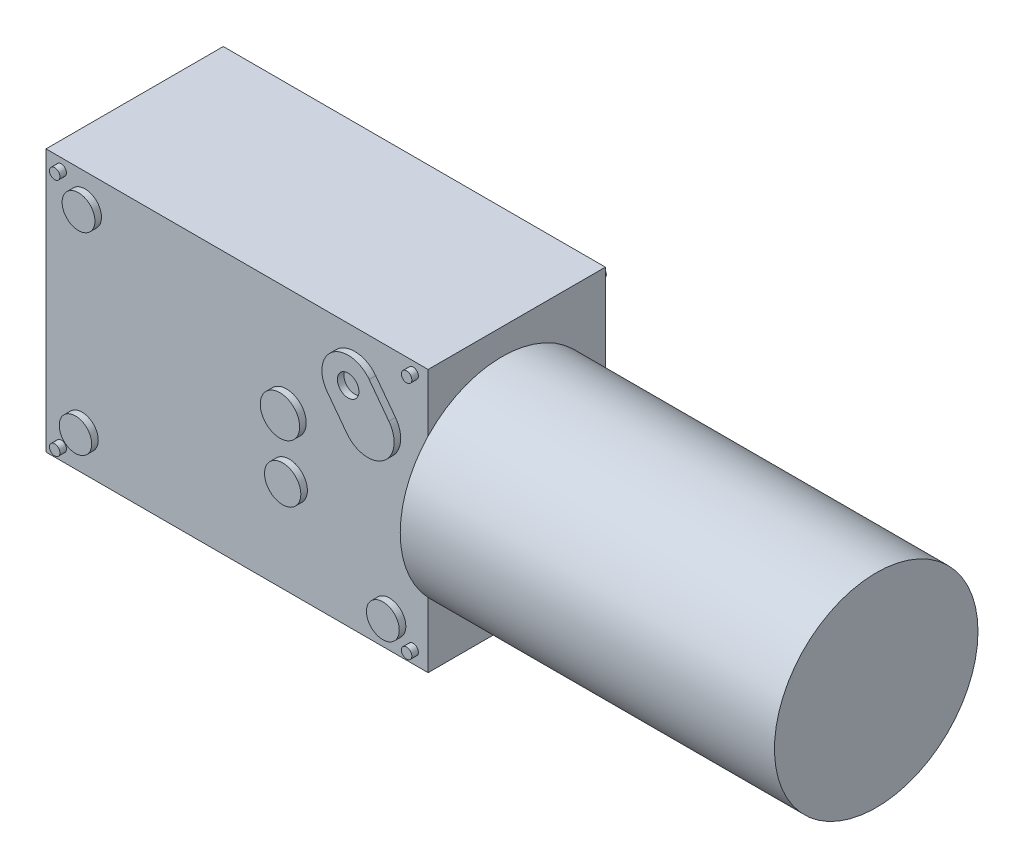
SolidWorks part; units mm, degrees
ref_plane "Plan de face" through (0, 0, 0) normal (0, 0, 1) x (1, 0, 0)
ref_plane "Plan de dessus" through (0, 0, 0) normal (0, 1, 0) x (1, 0, 0)
ref_plane "Plan de droite" through (0, 0, 0) normal (1, 0, 0) x (0, 0, -1)
sketch "Esquisse1" plane through (0, 0, 0) normal (0, 0, 1) x (1, 0, 0)
  line L1 (-30.3763, 14.7414) -> (27.8237, 14.7414)
  line L2 (-30.3763, 14.7414) -> (-30.3763, -25.2586)
  line L3 (-30.3763, -25.2586) -> (27.8237, -25.2586)
  line L4 (27.8237, 14.7414) -> (27.8237, -25.2586)
  dimension "D1" = 58.2
  dimension "D2" = 40
extrude "Boss.-Extru.1" add sketch "Esquisse1" along normal blind 27
sketch "Esquisse2" plane through (27.8237, 0, 0) normal (1, 0, 0) x (0, 0, -1)
  circle A0 centre (-15.7448, -4.6908) radius 15.5
  point P2 (-15.7448, -4.6908)
  dimension "D1" = 31
extrude "Boss.-Extru.2" add sketch "Esquisse2" along normal blind 57
sketch "Esquisse3" plane through (0, 0, 0) normal (0, 0, -1) x (-1, 0, 0)
  line L0 (-20.1036, 8.9894) -> (-17.1036, 4.9894) construction
  line L3 (-16.9036, 11.3894) -> (-13.9036, 7.3894)
  line L4 (-23.3036, 6.5894) -> (-20.3036, 2.5894)
  circle A0 centre (28.3939, 12.845) radius 0.797
  circle A1 centre (28.3939, -23.5849) radius 0.797
  circle A2 centre (-26.1689, 12.845) radius 0.797
  circle A3 centre (-26.1689, -23.5849) radius 0.797
  circle A4 centre (23.7192, 10.396) radius 3
  circle A5 centre (23.7192, -20.3195) radius 3
  circle A6 centre (-21.6906, -20.3195) radius 2.5
  arc A9 (-16.9036, 11.3894) -> (-23.3036, 6.5894) centre (-20.1036, 8.9894) ccw
  arc A10 (-20.3036, 2.5894) -> (-13.9036, 7.3894) centre (-17.1036, 4.9894) ccw
  circle A11 centre (-5.74, -0.085) radius 2.5
  circle A12 centre (-5.5699, -9.3874) radius 2.5
  circle A13 centre (-20.1036, 8.9894) radius 1.6438
  point P14 (-18.6036, 6.9894)
  point P21 (-22.5036, 12.1894)
  point P22 (-14.7036, 1.7894)
  point P23 (0, 0)
  point P26 (0, 0)
  dimension "D1" = 6
  dimension "D2" = 6
  dimension "D5" = 5
  dimension "D6" = 5
  dimension "D7" = 5
  dimension "D3" = 8
  dimension "D4" = 13
extrude "Boss.-Extru.3" add sketch "Esquisse3" along normal blind 1
sketch "Esquisse4" plane through (0, 0, 27) normal (0, 0, 1) x (1, 0, 0)
  line L0 (16.6446, 7.5331) -> (19.6446, 3.5331) construction
  line L1 (19.8446, 9.9331) -> (22.8446, 5.9331)
  line L2 (13.4446, 5.1331) -> (16.4446, 1.1331)
  circle A0 centre (25.5471, 13.1269) radius 0.797
  circle A1 centre (25.5471, -23.303) radius 0.797
  circle A2 centre (-28.0538, 13.1269) radius 0.797
  circle A3 centre (-28.0538, -23.303) radius 0.797
  circle A4 centre (6.2549, -1.6098) radius 3
  circle A5 centre (6.6712, -10.422) radius 2.7653
  circle A6 centre (-24.4256, 9.9328) radius 2.5
  arc A7 (19.8446, 9.9331) -> (13.4446, 5.1331) centre (16.6446, 7.5331) ccw
  arc A8 (16.4446, 1.1331) -> (22.8446, 5.9331) centre (19.6446, 3.5331) ccw
  circle A9 centre (21.9312, -20.8521) radius 2.5
  circle A10 centre (-24.8893, -19.7153) radius 2.4725
  circle A11 centre (16.6446, 7.5331) radius 1.6438
  point P14 (18.1446, 5.5331)
  point P21 (14.2446, 10.7331)
  point P22 (22.0446, 0.3331)
  point P29 (25.5471, 13.1269)
  point P30 (25.5471, -23.303)
  point P31 (-28.0538, -23.303)
  point P32 (-28.0538, 13.1269)
  point P33 (0, 0)
  point P34 (0, 0)
extrude "Boss.-Extru.4" add sketch "Esquisse4" along normal blind 1
sketch "Esquisse5" plane through (0, 0, 0) normal (0, 0, -1) x (-1, 0, 0)
  line L0 (30.3763, 14.7414) -> (30.3763, -25.2586) construction
  circle A0 centre (10.3763, -4.734) radius 8.5
  dimension "D1" = 17
  dimension "D2" = 20
extrude "Boss.-Extru.5" add sketch "Esquisse5" along normal blind 2
sketch "Esquisse6" plane through (0, 0, 0) normal (0, 0, -1) x (-1, 0, 0)
  circle A0 centre (10.3618, -4.723) radius 3.9141
  point P2 (10.3618, -4.723)
extrude "Boss.-Extru.6" add sketch "Esquisse6" along normal blind 13
